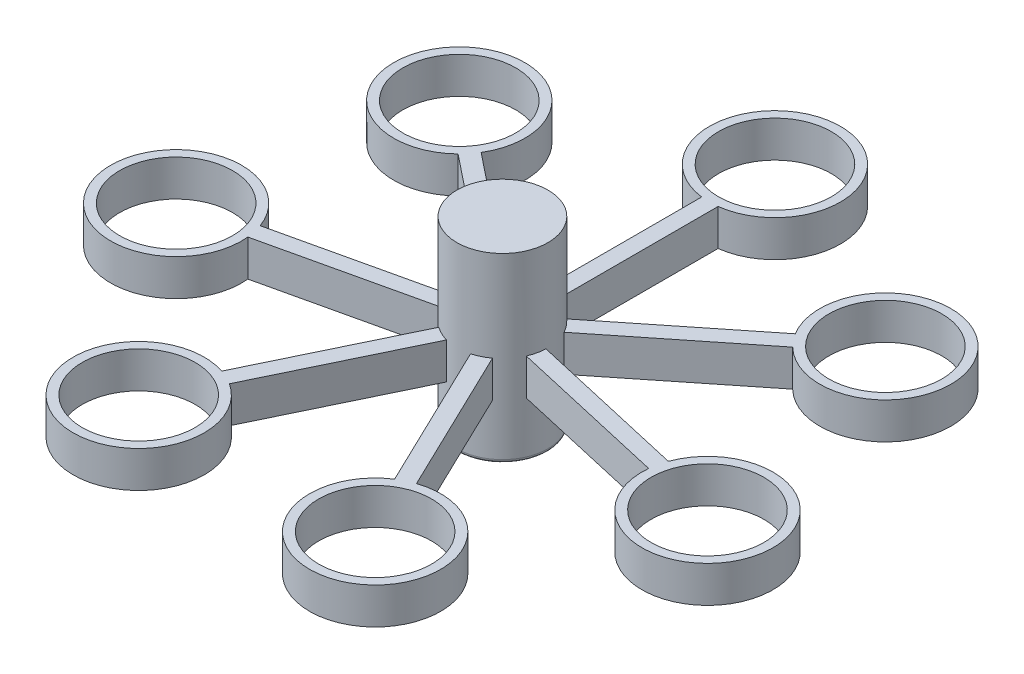
SolidWorks part; units mm, degrees
ref_plane "Front Plane" through (0, 0, 0) normal (0, 0, 1) x (1, 0, 0)
ref_plane "Top Plane" through (0, 0, 0) normal (0, 1, 0) x (1, 0, 0)
ref_plane "Right Plane" through (0, 0, 0) normal (1, 0, 0) x (0, 0, -1)
sketch "Sketch1" plane through (0, 0, 0) normal (0, 1, 0) x (1, 0, 0)
  circle A0 centre (0, 0) radius 12.5
  dimension "D1" = 25
extrude "Boss-Extrude1" add sketch "Sketch1" along normal blind 50
sketch "Sketch3" plane through (0, 0, 0) normal (0, 1, 0) x (1, 0, 0)
  line L3 (-2.2538, 56.9474) -> (-2.2538, 12.2951)
  line L4 (2.2538, 56.9474) -> (2.2538, 12.2951)
  line L5 (-2.2538, 12.2951) -> (2.2538, 12.2951)
  line L6 (0, 12.2951) -> (0, 0) construction
  arc A1 (2.2538, 56.9474) -> (-2.2538, 56.9474) centre (0, 74.8057) ccw
  circle A3 centre (0, 0) radius 12.5 construction
  circle A4 centre (0, 74.8057) radius 15.5
  point P11 (0, 12.2951)
  dimension "D1" = 18
  dimension "D2" = 31
extrude "Boss-Extrude2" add sketch "Sketch3" along normal blind 10 from offset 15
pattern_circular "CirPattern1" count 7 over 360 about axis through (0, 0, 0) along (0, 1, 0) of "Boss-Extrude2"
fillet "Fillet1" radius 1 1 edges at (0, 0, 12.5)
